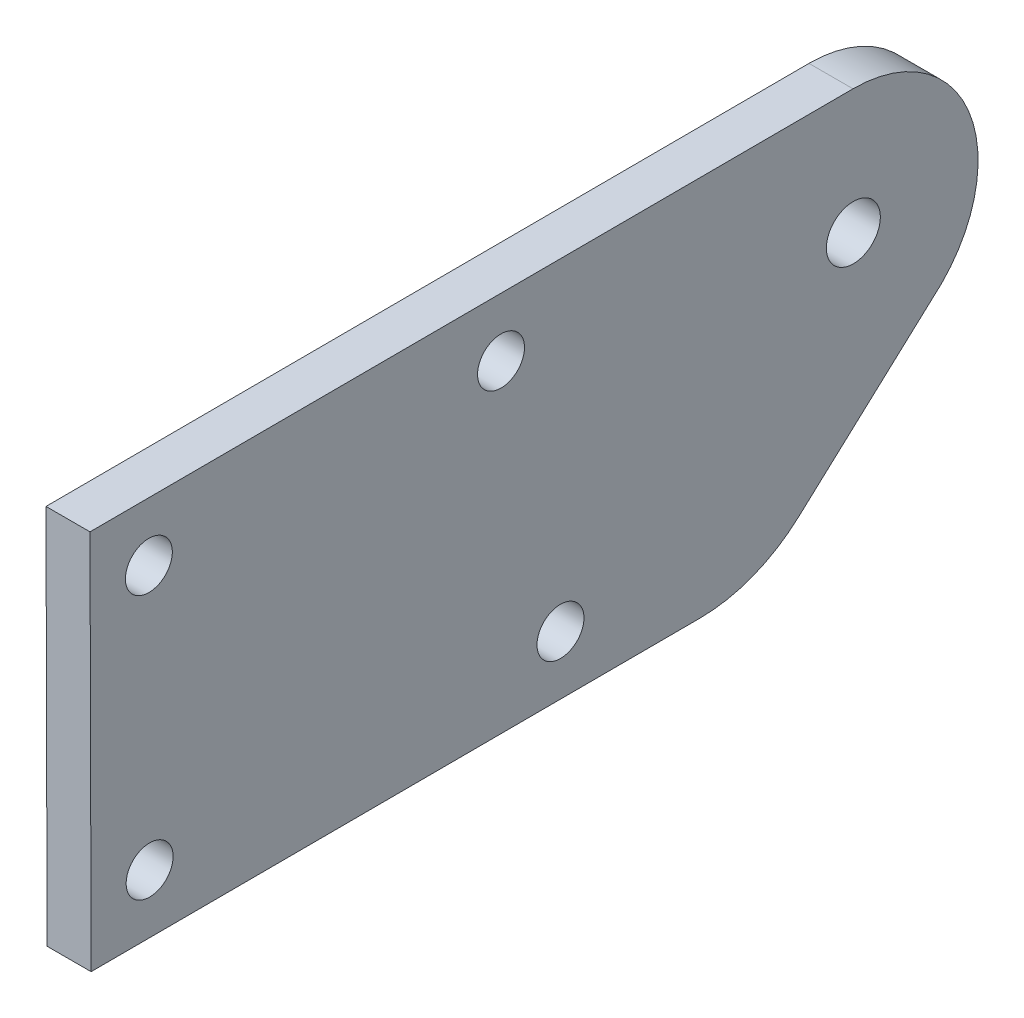
SolidWorks part; units mm, degrees
ref_plane "前视基准面" through (0, 0, 0) normal (0, 0, 1) x (1, 0, 0)
ref_plane "上视基准面" through (0, 0, 0) normal (0, 1, 0) x (1, 0, 0)
ref_plane "右视基准面" through (0, 0, 0) normal (1, 0, 0) x (0, 0, -1)
sketch "草图1" plane through (0, 0, 0) normal (1, 0, 0) x (0, 0, -1)
  line L47 (-51.9107, -17.7561) -> (-10.4109, -17.6369)
  line L48 (-3.6943, -15.0194) -> (6.0537, -6.1126)
  line L49 (-51.9854, 8.2438) -> (-51.9107, -17.7561)
  line L50 (-51.9854, 8.2438) -> (0.0144, 8.3932)
  circle A0 centre (0.0388, -0.1068) radius 1.8399
  circle A166 centre (-47.9739, 4.2553) radius 1.6
  arc A169 (6.0537, -6.1126) -> (0.0144, 8.3932) centre (0.0388, -0.1068) ccw
  circle A170 centre (-19.9223, -13.6642) radius 1.6
  circle A171 centre (-23.974, 4.3243) radius 1.6
  circle A175 centre (-47.9222, -13.7446) radius 1.6
  arc A176 (-10.4109, -17.6369) -> (-3.6943, -15.0194) centre (-10.4396, -7.6369) ccw
  point P0 (-150, 0)
  point P1 (135, 0)
  point P9 (-344.9533, 138.7825)
  point P10 (187.1329, 101.1747)
  point P11 (165.9429, -19)
  point P12 (-156.9154, -19)
  dimension "D7" = 4
  dimension "D8" = 22
  dimension "D9" = 52
  dimension "D10" = 8.5
  dimension "D4" = 4
  dimension "D11" = 52
  dimension "D12" = 41.5
  dimension "D13" = 26
  dimension "D6" = 28
  dimension "D5" = 4
  dimension "D2" = 18
  dimension "D1" = 24
  dimension "D3" = 4
extrude "凸台-拉伸1" add sketch "草图1" along normal blind 3
